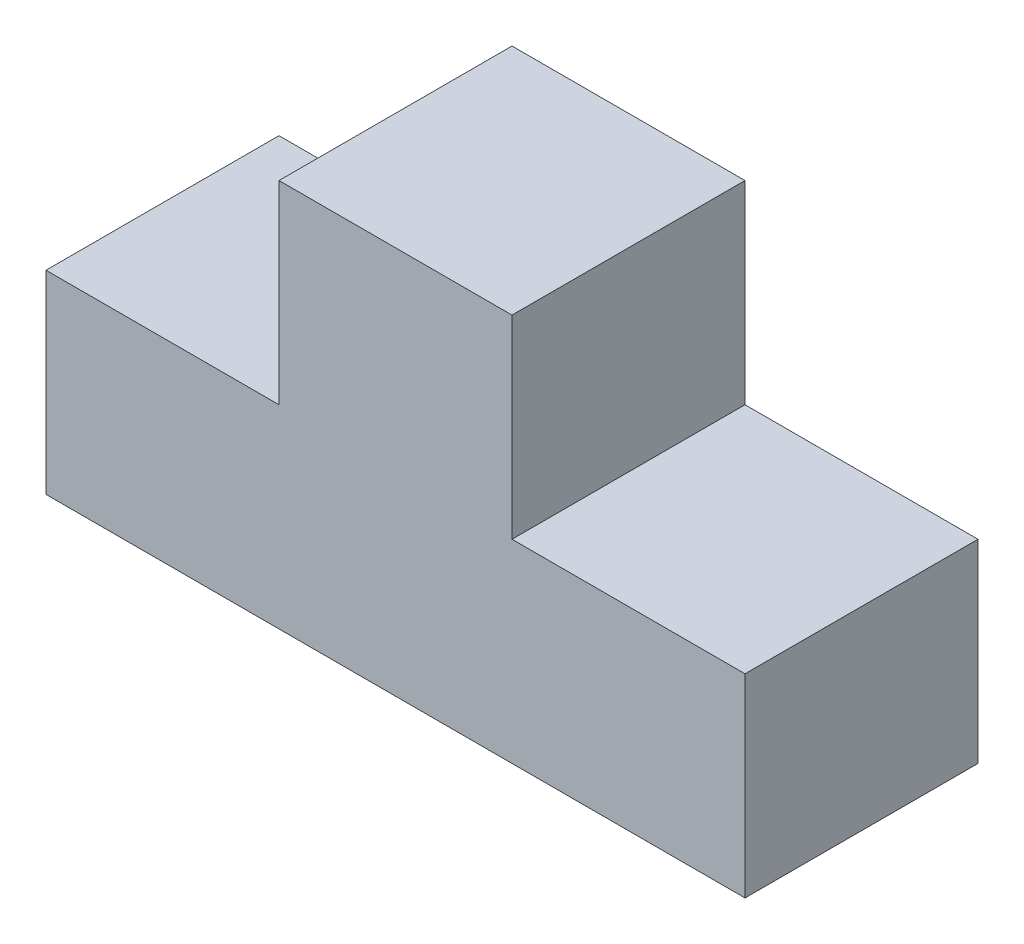
SolidWorks part; units mm, degrees
ref_plane "Front Plane" through (0, 0, 0) normal (0, 0, 1) x (1, 0, 0)
ref_plane "Top Plane" through (0, 0, 0) normal (0, 1, 0) x (1, 0, 0)
ref_plane "Right Plane" through (0, 0, 0) normal (1, 0, 0) x (0, 0, -1)
sketch "Sketch2" plane through (0, 0, 0) normal (0, 0, 1) x (1, 0, 0)
  line L0 (-45, 0) -> (45, 0)
  line L1 (45, 0) -> (45, 25)
  line L2 (45, 25) -> (15, 25)
  line L3 (15, 25) -> (15, 50)
  line L4 (15, 50) -> (-15, 50)
  line L5 (0, 0) -> (0, 50) construction
  line L6 (-15, 25) -> (-15, 50)
  line L7 (-45, 25) -> (-15, 25)
  line L8 (-45, 0) -> (-45, 25)
  dimension "D1" = 45
  dimension "D2" = 25
  dimension "D3" = 30
  dimension "D4" = 25
  dimension "D5" = 15
extrude "Boss-Extrude1" add sketch "Sketch2" along normal blind 30
